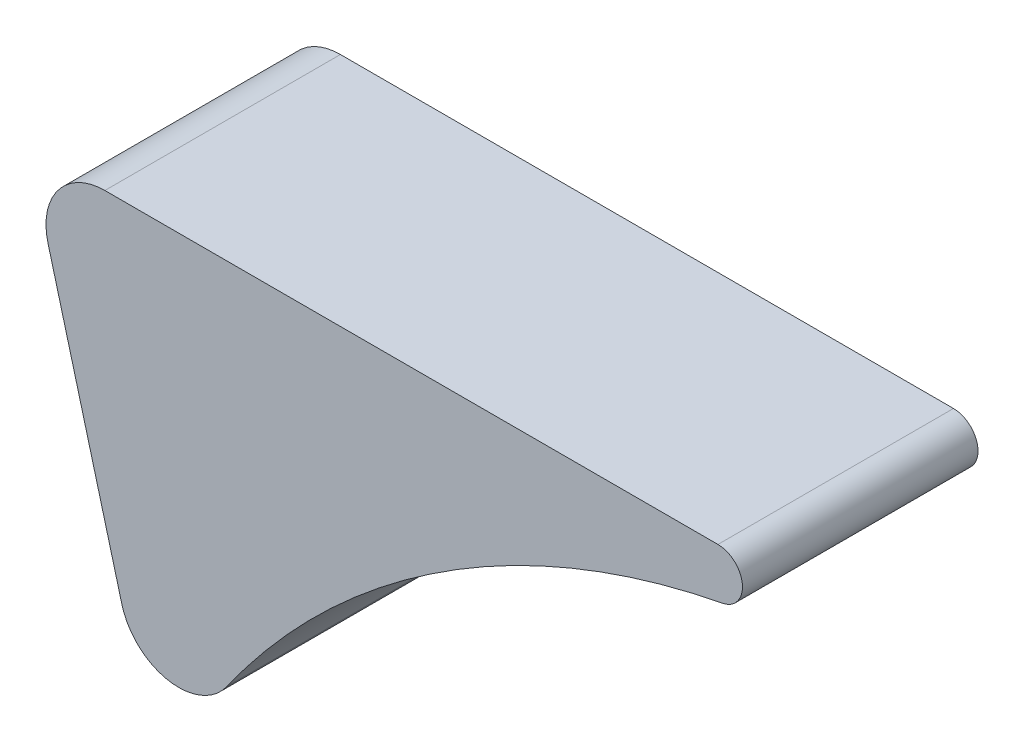
SolidWorks part; units mm, degrees
ref_plane "Plane1" through (0, 0, 0) normal (0, 0, 1) x (1, 0, 0)
ref_plane "Plane2" through (0, 0, 0) normal (0, 1, 0) x (1, 0, 0)
ref_plane "Plane3" through (0, 0, 0) normal (1, 0, 0) x (0, 0, -1)
sketch "Sketch1" plane through (0, 0, 0) normal (0, 0, 1) x (1, 0, 0)
  line L0 (-38.224, 24.1759) -> (-41.9881, 38.2235)
  line L1 (-39.0903, 42) -> (-7.8541, 42)
  arc A0 (-7.6176, 39.5226) -> (-32.8759, 23.2215) centre (0, 0) ccw
  arc A1 (-7.8541, 42) -> (-7.6176, 39.5226) centre (-7.8541, 40.75) cw
  arc A2 (-41.9881, 38.2235) -> (-39.0903, 42) centre (-39.0903, 39) cw
  arc A3 (-32.8759, 23.2215) -> (-38.224, 24.1759) centre (-35.3263, 24.9523) cw
  point P9 (-43, 42)
  dimension "D1" = 40.25
  dimension "D2" = 1.25
  dimension "D6" = 3
  dimension "D3" = 42
  dimension "D4" = 43
  dimension "D5" = 75
extrude "Extrude1" add sketch "Sketch1" along normal mid plane 12
